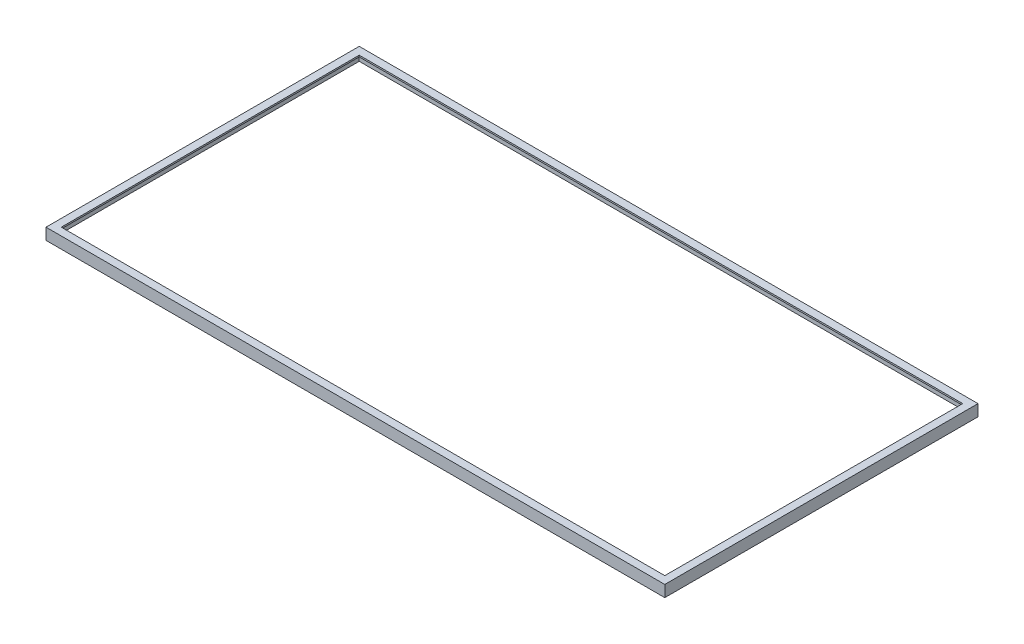
SolidWorks part; units mm, degrees
ref_plane "Front Plane" through (0, 0, 0) normal (0, 0, 1) x (1, 0, 0)
ref_plane "Top Plane" through (0, 0, 0) normal (0, 1, 0) x (1, 0, 0)
ref_plane "Right Plane" through (0, 0, 0) normal (1, 0, 0) x (0, 0, -1)
sketch "Sketch1" plane through (0, 0, 0) normal (0, 1, 0) x (1, 0, 0)
  line L1 (0, 0) -> (810, 0)
  line L2 (0, 0) -> (0, 410)
  line L3 (0, 410) -> (810, 410)
  line L4 (810, 0) -> (810, 410)
  dimension "D1" = 410
  dimension "D2" = 810
extrude "Boss-Extrude1" add sketch "Sketch1" along normal blind 15
shell "Shell1" thickness 2
sketch "Sketch2" plane through (0, 15, 0) normal (0, 1, 0) x (1, 0, 0)
  line L0 (0, 0) -> (810, 0) construction
  line L1 (10, 400) -> (800, 400)
  line L2 (10, 400) -> (10, 10)
  line L3 (10, 10) -> (800, 10)
  line L4 (800, 400) -> (800, 10)
  line L5 (0, 410) -> (0, 0) construction
  dimension "D1" = 390
  dimension "D2" = 790
  dimension "D3" = 10
  dimension "D4" = 10
extrude "Cut-Extrude1" cut sketch "Sketch2" against normal blind 15
